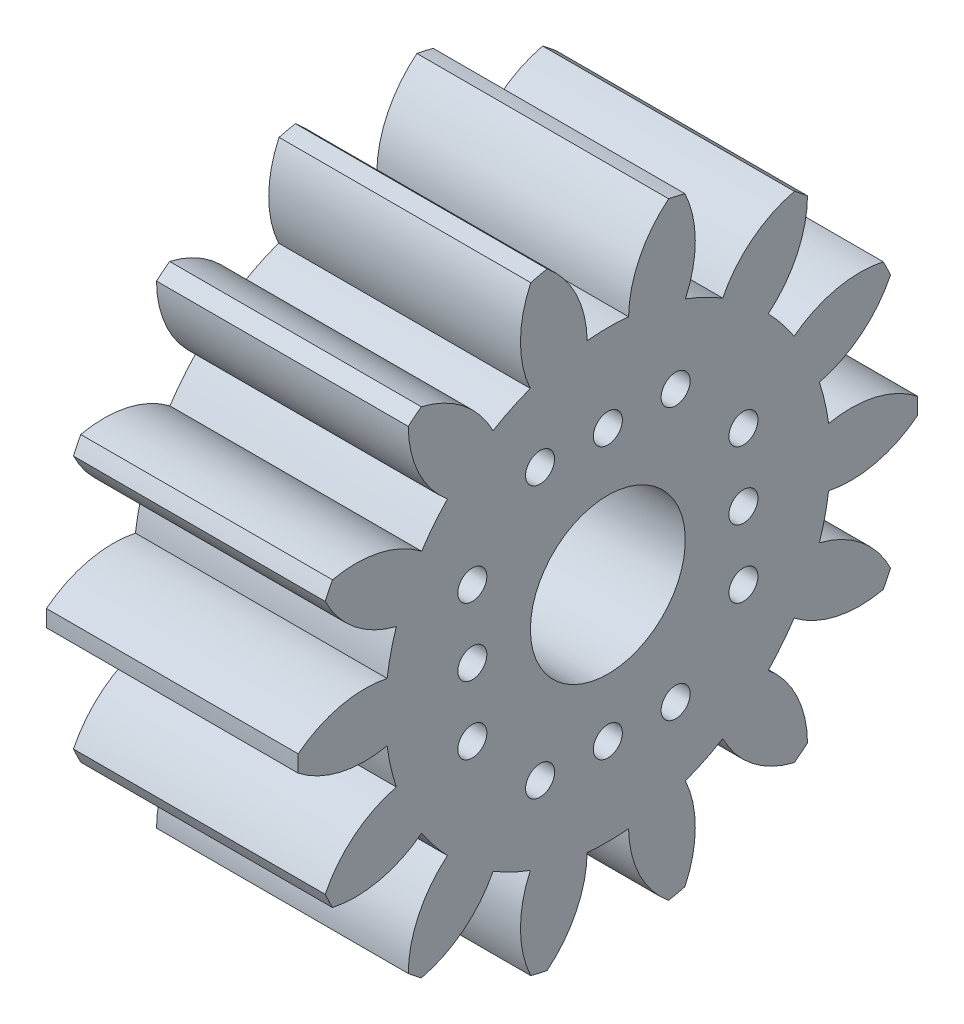
SolidWorks part; units mm, degrees
ref_plane "Plane1" through (0, 0, 0) normal (0, 0, 1) x (1, 0, 0)
ref_plane "Plane2" through (0, 0, 0) normal (0, 1, 0) x (1, 0, 0)
ref_plane "Plane3" through (0, 0, 0) normal (1, 0, 0) x (0, 0, -1)
sketch "HoldingSke" plane through (0, 0, 0) normal (0, 1, 0) x (1, 0, 0)
  line L0 (0, 0) -> (0.4851, -0.121)
  line L1 (-15, 0) -> (100, 0) construction
  line L2 (0, 0) -> (-2.1039, 2.3779)
  line L3 (0, 0) -> (-11.863, 4.5341)
  line L4 (0, 0) -> (8.3795, 2.0892)
  line L5 (0, 0) -> (-46.8476, -17.4728)
  line L6 (0, 0) -> (-13.2634, -8.9489)
  line L7 (-2.1039, 2.3779) -> (8.6587, 51.2064)
  line L8 (-76.2, 54.61) -> (-74.8, 54.61)
  line L9 (-71.009, 38.7566) -> (-53.1078, 45.2721)
  line L10 (-76.2, 71.12) -> (104.1128, 71.12)
  line L11 (0, 0) -> (-16, 0)
  line L12 (-76.2, 101.6) -> (-76.133, 101.6)
  line L13 (24.9733, 27.94) -> (52.9518, 28.4284)
  line L14 (24.9733, 27.94) -> (24.9743, 27.94)
  line L15 (24.9733, 27.94) -> (100.4006, 29.5858)
  line L16 (-63.627, -2) -> (-12.827, -2)
  circle A0 centre (0, 0) radius 4
  circle A1 centre (0, 0) radius 11.499
  circle A2 centre (0, 0) radius 37.5
  circle A3 centre (0, 0) radius 4
  dimension "MHD" = 22.998
  dimension "Hub_dia" = 75
  dimension "Bore" = 8
  dimension "MBD" = 8
  dimension "Num_teeth" = 14
  dimension "Pitch_radius" = 180.3128
  dimension "Pitch" = 0.5
  dimension "Width" = 16
  dimension "Overall_len" = 50
  dimension "Show_teeth" = 14
  dimension "Thickness" = 16
  dimension "OAL" = 50.0006
  dimension "T_dim" = 1.4
  dimension "Ap" = 20
  dimension "H" = 19.05
  dimension "Backlash" = 0.067
  dimension "Addendum_fac" = 1
  dimension "Dedendum_fac" = 1.25
  dimension "Clearance_fac" = 0.25
  dimension "Dedendum_add" = 0.001
  dimension "Module" = 2
sketch "BasProSke" plane through (0, 0, 0) normal (0, 1, 0) x (1, 0, 0)
  line L0 (-10, 0) -> (60, 0) construction
  line L1 (0, 0) -> (0, 16)
  line L2 (0, 0) -> (13, 0)
  line L3 (13, 0) -> (13, 16)
  line L4 (13, 16) -> (0, 16)
  dimension "Diameter" = 32
  dimension "Thickness" = 13
revolve "Base-Revolve" add sketch "BasProSke" angle 360 about L0
sketch "TooCutSke" plane through (0, 0, 0) normal (1, 0, 0) x (0, 0, -1)
  line L1 (0, 0) -> (0, 107) construction
  line L2 (0, 0) -> (-1.6846, 13.8983) construction
  line L3 (0, 0) -> (-6.1971, 27.1511) construction
  line L4 (-1.6846, 13.8983) -> (-3.0985, 13.5756) construction
  arc A0 (1.0679, 11.4493) -> (-1.0679, 11.4493) centre (0, 0) ccw
  arc A1 (3.1634, 15.7101) -> (-3.1634, 15.7101) centre (0, 0) ccw
  circle A2 centre (0, 0) radius 14 construction
  circle A3 centre (0, 0) radius 13.1557 construction
  arc A4 (-1.0679, 11.4493) -> (-3.1634, 15.7101) centre (-6.6668, 11.3413) ccw
  arc A5 (3.1634, 15.7101) -> (1.0679, 11.4493) centre (6.6668, 11.3413) ccw
  dimension "Root_dia" = 22.998
  dimension "Overcut_dia" = 32.0508
  dimension "Pitch_dia" = 28
  dimension "Base_dia" = 26.3114
  dimension "Flank_rad" = 5.6
  dimension "Half_ang" = 12.857
  dimension "Half_CT" = 1.4503
extrude "ToothCut" cut sketch "TooCutSke" along normal through all
fillet "Breaks" [suppressed] radius 0.04
fillet "RootFillets" [suppressed] radius 0.501
pattern_circular "TeethCuts" count 14 every 25.714 about axis through (-10, 0, 0) along (1, 0, 0) of "ToothCut", "RootFillets", "Breaks"
sketch "HubNeaOneSke" plane through (0, 0, 0) normal (-1, 0, 0) x (0, 0, 1)
  circle A0 centre (0, 0) radius 11.499
  dimension "Diameter" = 22.998
extrude "HubNearOne" [suppressed] add sketch "HubNeaOneSke" along normal blind 37.0006
sketch "HubNeaBotSke" plane through (0, 0, 0) normal (-1, 0, 0) x (0, 0, 1)
  circle A0 centre (0, 0) radius 11.499
  dimension "Diameter" = 22.998
extrude "HubNearBoth" [suppressed] add sketch "HubNeaBotSke" along normal blind 18.5003
ref_plane "FarPln" through (13, 0, 0) normal (1, 0, 0) x (0, 0, -1)
sketch "HubFarSke" plane through (13, 0, 0) normal (1, 0, 0) x (0, 0, -1)
  circle A0 centre (0, 0) radius 11.499
  dimension "Diameter" = 22.998
extrude "HubFar" [suppressed] add sketch "HubFarSke" along normal blind 18.5003
sketch "BorSke" plane through (0, 0, 0) normal (1, 0, 0) x (0, 0, -1)
  circle A0 centre (0, 0) radius 4
  dimension "Diameter" = 8
extrude "Bore" cut sketch "BorSke" along normal mid plane 100.0011
sketch "KeySke" plane through (0, 0, 0) normal (1, 0, 0) x (0, 0, -1)
  line L0 (-1.5, 0) -> (-1.5, 5.4)
  line L1 (-1.5, 5.4) -> (1.5, 5.4)
  line L2 (1.5, 5.4) -> (1.5, 0)
  line L3 (0, 0) -> (0, 34) construction
  line L4 (-1.5, 0) -> (1.5, 0)
  dimension "Offset" = 5.4
  dimension "Width" = 3
extrude "Keyway" [suppressed] cut sketch "KeySke" along normal mid plane 100.0011
pattern_circular "Keyway2" [suppressed] count 2 every 90 about axis through (-10, 0, 0) along (1, 0, 0)
sketch "Sketch2" plane through (13, 0, 0) normal (1, 0, 0) x (0, 0, -1)
  line L0 (-3.5, 7) -> (0, 7) construction
  line L1 (0, 7) -> (3.5, 7) construction
  line L2 (0, 0) -> (0, 7) construction
  circle A0 centre (-3.5, 7) radius 0.75
  circle A1 centre (0, 7) radius 0.75
  circle A2 centre (3.5, 7) radius 0.75
  dimension "D1" = 1.5
  dimension "D2" = 7
  dimension "D3" = 7
extrude "Cut-Extrude1" cut sketch "Sketch2" against normal blind 6
pattern_circular "CirPattern1" count 4 over 360 about axis through (0, 0, 0) along (1, 0, 0) of "Cut-Extrude1"
equation "' \"Module@HoldingSke\" = 6.35"
equation "' \"Num_teeth@HoldingSke\" = 12"
equation "' \"Ap@HoldingSke\" =  20"
equation "' \"Width@HoldingSke\" = 0.5 * 25.4"
equation "' \"Hub_dia@HoldingSke\"= 1 * 25.4"
equation "' \"Overall_len@HoldingSke\" = 1.0 * 25.4"
equation "' \"Bore@HoldingSke\" = 0.75 * 25.4"
equation "' \"T_dim@HoldingSke\" = 0.1 * 25.4"
equation "' \"Width@KeySke\" = 0.25 * 25.4"
equation "' \"Show_teeth@HoldingSke\" = 13"
equation "' \"Backlash@HoldingSke\" = 0.009 * 25.4"
equation "' \"Addendum_fac@HoldingSke\" = 1.0"
equation "' \"Dedendum_fac@HoldingSke\" = 1.25"
equation "' \"Dedendum_add@HoldingSke\" = 0.00005 * 25.4"
equation "' \"Clearance_fac@HoldingSke\" = 0.25"
equation "\"Pitch@HoldingSke\" = 1 / \"Module@HoldingSke\""
equation "\"Overcut_dia@TooCutSke\" = (\"Num_teeth@HoldingSke\" + 2 * \"Addendum_fac@HoldingSke\") / \"Pitch@HoldingSke\" + 0.002 * 25.4"
equation "\"Pitch_dia@TooCutSke\" = \"Num_teeth@HoldingSke\" / \"Pitch@HoldingSke\""
equation "\"Base_dia@TooCutSke\" = \"Num_teeth@HoldingSke\" / \"Pitch@HoldingSke\" * cos((\"Ap@HoldingSke\"  * 3.14159265 / 180))"
equation "\"Root_dia@TooCutSke\" = (\"Num_teeth@HoldingSke\" + 2) / \"Pitch@HoldingSke\" - 2 * (\"Addendum_fac@HoldingSke\" + \"Dedendum_fac@HoldingSke\") / \"Pitch@HoldingSke\" - \"Dedendum_add@HoldingSke\" * 2"
equation "\"Half_ang@TooCutSke\" = 180 / \"Num_teeth@HoldingSke\""
equation "\"Half_CT@TooCutSke\" = \"Num_teeth@HoldingSke\" / \"Pitch@HoldingSke\" * sin((3.14159265 / 2 / \"Num_teeth@HoldingSke\")) / 2 - 7 * \"Backlash@HoldingSke\" / 4"
equation "\"Flank_rad@TooCutSke\" = \"Num_teeth@HoldingSke\" / \"Pitch@HoldingSke\" / 5"
equation "\"Radius@RootFillets\" = \"Clearance_fac@HoldingSke\" / \"Pitch@HoldingSke\" + \"Dedendum_add@HoldingSke\""
equation "\"Break_rad@Breaks\" = 0.02 / \"Pitch@HoldingSke\""
equation "\"Thickness@HoldingSke\" = \"Width@HoldingSke\""
equation "\"OAL@HoldingSke\" = \"Thickness@HoldingSke\""
equation "\"MHD@HoldingSke\" = (\"Num_teeth@HoldingSke\" + 2) / \"Pitch@HoldingSke\" - 2 * (\"Addendum_fac@HoldingSke\" + \"Dedendum_fac@HoldingSke\")  / \"Pitch@HoldingSke\" - \"Dedendum_add@HoldingSke\" * 2"
equation "\"MBD@HoldingSke\" = (\"Num_teeth@HoldingSke\" + 2) / \"Pitch@HoldingSke\" - 2 * (\"Addendum_fac@HoldingSke\" + \"Dedendum_fac@HoldingSke\")  / \"Pitch@HoldingSke\" - \"Dedendum_add@HoldingSke\" * 2 - 0.002 * 25.4"
equation "\"MHD@HoldingSke\" = ((sgn( \"MHD@HoldingSke\" - \"Hub_dia@HoldingSke\" )-1)*( \"MHD@HoldingSke\" - \"Hub_dia@HoldingSke\" ))/-2+ \"Hub_dia@HoldingSke\""
equation "\"MBD@HoldingSke\" = ((sgn( \"MBD@HoldingSke\" - \"Bore@HoldingSke\" )-1)*( \"MBD@HoldingSke\" - \"Bore@HoldingSke\" ))/-2+ \"Bore@HoldingSke\""
equation "\"OAL@HoldingSke\" = ((sgn( \"OAL@HoldingSke\" - \"Overall_len@HoldingSke\" )+1)*( \"OAL@HoldingSke\" - \"Overall_len@HoldingSke\" ))/2 + \"Overall_len@HoldingSke\" + 0.000002 * 25.4"
equation "\"Num_teeth@TeethCuts\" = int( \"Show_teeth@HoldingSke\" ) + 1"
equation "\"Num_teeth@TeethCuts\" = ((sgn( \"Num_teeth@TeethCuts\" - \"Num_teeth@HoldingSke\" )-1)*( \"Num_teeth@TeethCuts\" - \"Num_teeth@HoldingSke\" ))/-2+ \"Num_teeth@HoldingSke\""
equation "\"Num_teeth@TeethCuts\" = ((sgn( \"Num_teeth@TeethCuts\" - 2.0)+1)*( \"Num_teeth@TeethCuts\" - 2.0))/2 +2.0"
equation "\"Angle@TeethCuts\" = 360.0 / \"Num_teeth@HoldingSke\""
equation "\"Diameter@BasProSke\" = (\"Num_teeth@HoldingSke\" + 2 * \"Addendum_fac@HoldingSke\") / \"Pitch@HoldingSke\""
equation "' \"Fillet_rad@BasProSke\" =  \"Thickness@HoldingSke\" * 0.05"
equation "\"MHD@HoldingSke\" = ((sgn( \"MHD@HoldingSke\" - \"Root_dia@TooCutSke\" )-1)*( \"MHD@HoldingSke\" - \"Root_dia@TooCutSke\" ))/-2+ \"Root_dia@TooCutSke\""
equation "\"Diameter@HubNeaOneSke\" = \"MHD@HoldingSke\""
equation "\"Length@HubNearOne\" = \"OAL@HoldingSke\" - \"Thickness@BasProSke\""
equation "\"Diameter@HubNeaBotSke\" = \"MHD@HoldingSke\""
equation "\"Length@HubNearBoth\" = ( \"OAL@HoldingSke\" - \"Thickness@BasProSke\" ) / 2.0"
equation "\"Thickness@FarPln\" = \"Thickness@BasProSke\""
equation "\"Diameter@HubFarSke\" = \"MHD@HoldingSke\""
equation "\"Length@HubFar\" = ( \"OAL@HoldingSke\" - \"Thickness@BasProSke\" ) / 2.0"
equation "\"Diameter@BorSke\" = \"MBD@HoldingSke\""
equation "\"D1@Bore\" = \"OAL@HoldingSke\" * 2.0"
equation "\"D1@Keyway\" = \"OAL@HoldingSke\" * 2.0"
equation "\"Offset@KeySke\" = \"T_dim@HoldingSke\" + \"MBD@HoldingSke\" / 2.0"
